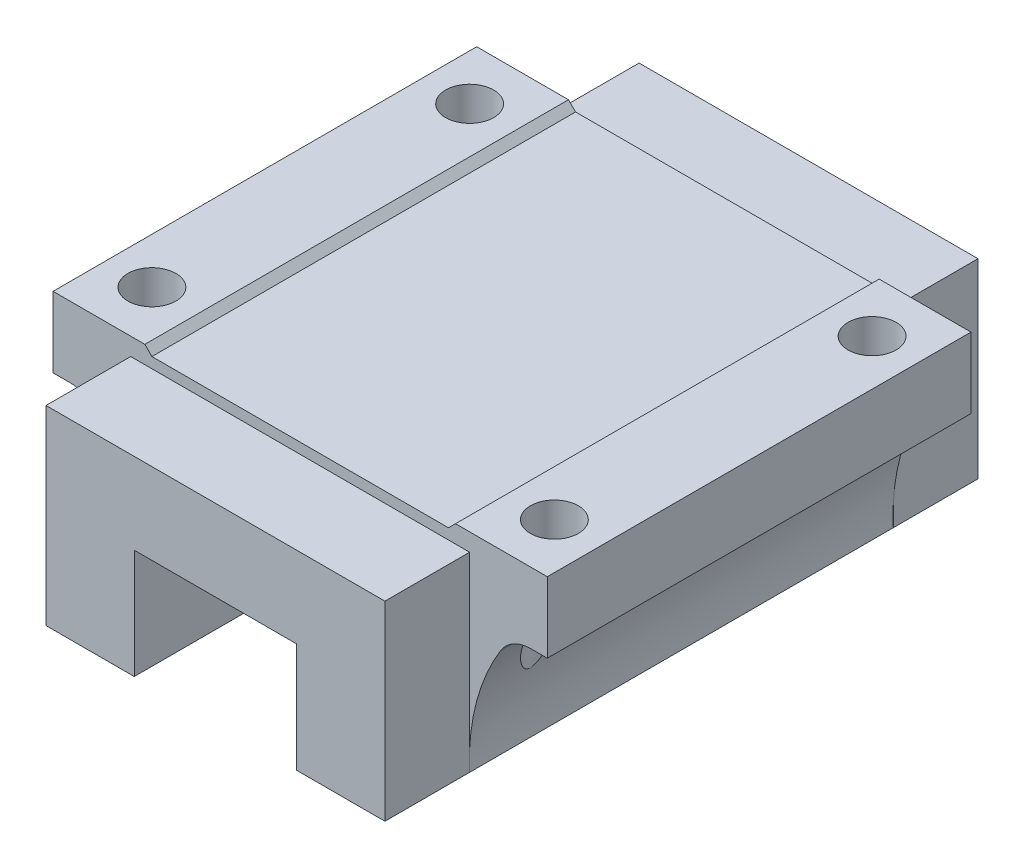
SolidWorks part; units mm, degrees
material "A3钢"
ref_plane "前视基准面" through (0, 0, 0) normal (0, 0, 1) x (1, 0, 0)
ref_plane "上视基准面" through (0, 0, 0) normal (0, 1, 0) x (1, 0, 0)
ref_plane "右视基准面" through (0, 0, 0) normal (1, 0, 0) x (0, 0, -1)
sketch "草图1" plane through (0, 0, 0) normal (0, 0, 1) x (1, 0, 0)
  line L0 (-21, 0) -> (21, 0)
  line L1 (-21, 0) -> (-22, 1)
  line L2 (-22, 1) -> (-35, 1)
  line L3 (-35, 1) -> (-35, -9)
  line L4 (-35, -9) -> (-32.6392, -9)
  line L6 (-24, -28.5) -> (-11.5, -28.5)
  line L7 (-11.5, -28.5) -> (-11.5, -13)
  line L8 (-11.5, -13) -> (11.5, -13)
  line L9 (0, 3.4321) -> (0, -8.0247) construction
  line L10 (11.5, -28.5) -> (11.5, -13)
  line L11 (24, -28.5) -> (11.5, -28.5)
  line L13 (35, -9) -> (32.6392, -9)
  line L14 (35, 1) -> (35, -9)
  line L15 (22, 1) -> (35, 1)
  line L16 (21, 0) -> (22, 1)
  arc A0 (-28.3741, -11.3906) -> (-24, -28.5) centre (-53.9648, -27.0469) cw
  arc A1 (28.3741, -11.3906) -> (24, -28.5) centre (53.9648, -27.0469) ccw
  arc A2 (32.6392, -9) -> (28.3741, -11.3906) centre (32.6392, -14) ccw
  arc A3 (-28.3741, -11.3906) -> (-32.6392, -9) centre (-32.6392, -14) ccw
  point P23 (30, -9)
  point P26 (-30, -9)
  dimension "D11" = 30
  dimension "D12" = 5
  dimension "D1" = 1
  dimension "D2" = 70
  dimension "D3" = 29.5
  dimension "D4" = 10
  dimension "D5" = 23
  dimension "D6" = 15.5
  dimension "D7" = 42
  dimension "D8" = 1
  dimension "D9" = 48
  dimension "D10" = 5
extrude "凸台-拉伸1" add sketch "草图1" along normal mid plane 60
hole_wizard "M8 螺纹孔1" positions "草图2" profile "草图3" tap size "M8" standard "GB" end condition through all
sketch "草图2" plane through (0, 1, 0) normal (0, 1, 0) x (1, 0, 0)
  line L0 (-42.4501, 0) -> (44.5002, 0) construction
  line L3 (0, 37.6865) -> (0, -38.5307) construction
  point P0 (-28.5, 22.5)
  point P15 (28.5, 22.5)
  point P16 (28.5, -22.5)
  point P17 (-28.5, -22.5)
  dimension "D1" = 45
  dimension "D2" = 57
sketch "草图3" plane through (-28.5, 1, -22.5) normal (1, 0, 0) x (0, 0, 1)
  line L0 (0, 0) -> (0, 29.5)
  line L1 (0, 29.5) -> (3.4, 29.5)
  line L2 (3.4, 29.5) -> (3.4, 0)
  line L5 (3.4, 0) -> (0, 0)
  line L11 (0, -6.35) -> (0, 107.95) construction
  dimension "通孔螺纹孔钻头直径" = 6.8
  dimension "通孔螺纹孔钻头深度" = 29.5
cosmetic thread "孔螺蚊线1" parameters "D2"=8
cosmetic thread "孔螺蚊线2" parameters "D2"=8
cosmetic thread "孔螺蚊线3" parameters "D2"=8
cosmetic thread "孔螺蚊线4" parameters "D2"=8
sketch "草图4" plane through (0, 0, 30) normal (0, 0, 1) x (1, 0, 0)
  line L0 (-11.5, -28.5) -> (-11.5, -13)
  line L1 (-11.5, -13) -> (11.5, -13)
  line L2 (11.5, -13) -> (11.5, -28.5)
  line L3 (11.5, -28.5) -> (24, -28.5)
  line L4 (24, -28.5) -> (24, -1.5)
  line L5 (24, -1.5) -> (-24, -1.5)
  line L6 (-24, -1.5) -> (-24, -28.5)
  line L7 (-24, -28.5) -> (-11.5, -28.5)
  dimension "D1" = 27
extrude "凸台-拉伸2" add sketch "草图4" along normal blind 12
mirror "镜向1" about plane through (0, 0, 0) normal (0, 0, 1) of "凸台-拉伸2"
